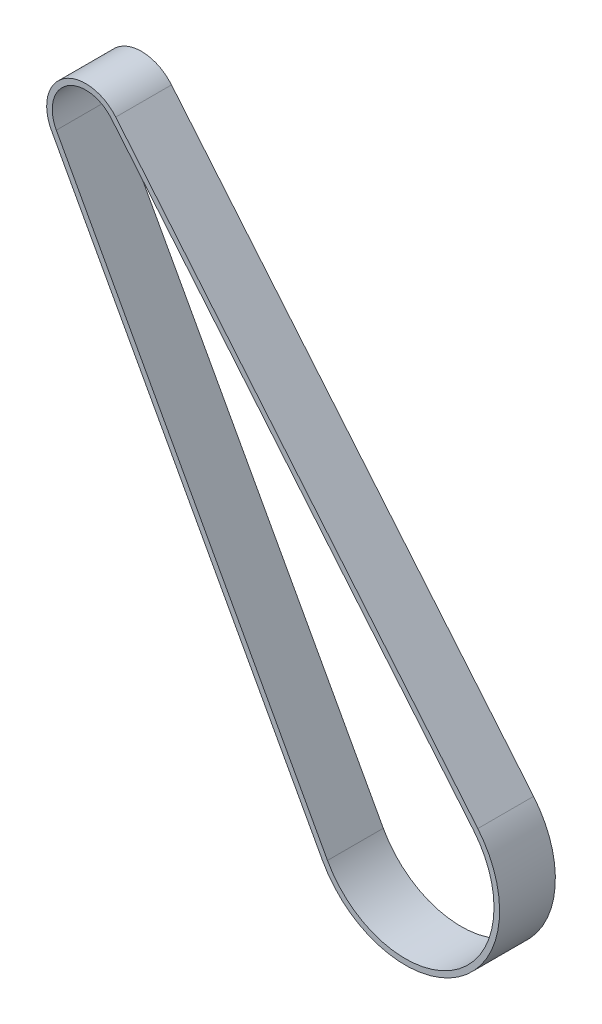
SolidWorks part; units mm, degrees
ref_plane "Plan de face" through (0, 0, 0) normal (0, 0, 1) x (1, 0, 0)
ref_plane "Plan de dessus" through (0, 0, 0) normal (0, 1, 0) x (1, 0, 0)
ref_plane "Plan de droite" through (0, 0, 0) normal (1, 0, 0) x (0, 0, -1)
sketch "Esquisse2" plane through (0, 0, 0) normal (0, 0, 1) x (1, 0, 0)
  line L0 (0, 0) -> (1, 0) construction
  line L1 (0, 0) -> (0, 1) construction
  line L2 (5.3808, 4.4774) -> (70.3004, -73.5402)
  line L3 (42.4749, -92.4456) -> (-6.1446, -3.3532)
  arc A0 (-6.1446, -3.3532) -> (5.3808, 4.4774) centre (0, 0) cw
  arc A1 (70.3004, -73.5402) -> (42.4749, -92.4456) centre (57.3096, -84.35) cw
extrude "Extru.-Mince1" add sketch "Esquisse2" along normal blind 10 thin
